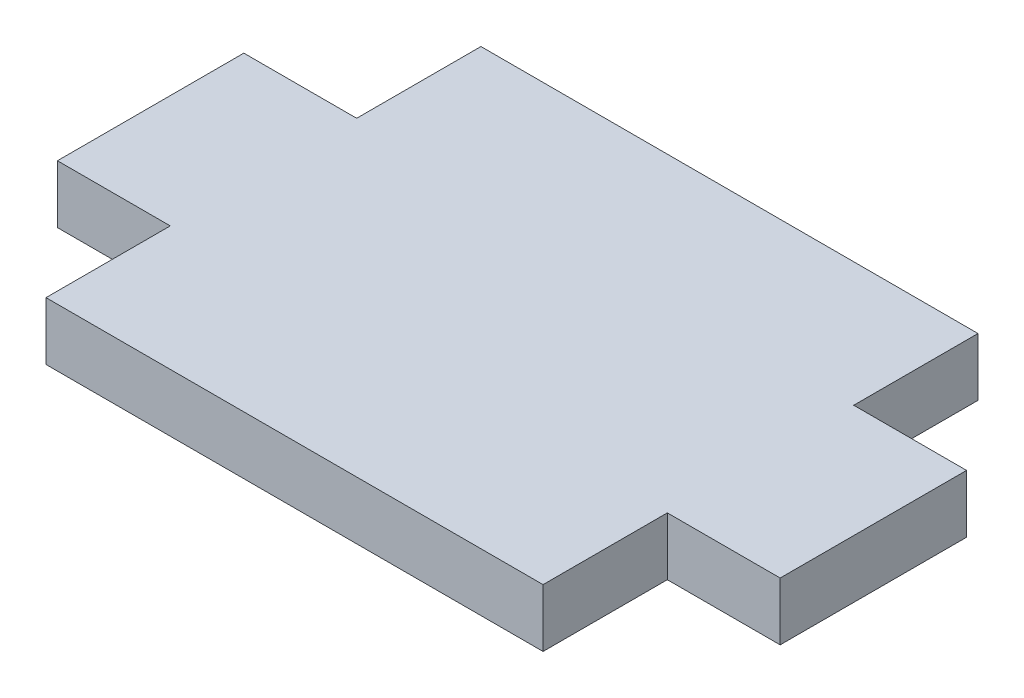
SolidWorks part; units mm, degrees
ref_plane "Front Plane" through (0, 0, 0) normal (0, 0, 1) x (1, 0, 0)
ref_plane "Top Plane" through (0, 0, 0) normal (0, 1, 0) x (1, 0, 0)
ref_plane "Right Plane" through (0, 0, 0) normal (1, 0, 0) x (0, 0, -1)
sketch "Sketch1" plane through (0, 0, 0) normal (0, 1, 0) x (1, 0, 0)
  line L0 (0, 4.0447) -> (0, -2.5708) construction
  line L1 (-12.7, 11.1125) -> (12.7, 11.1125)
  line L2 (-12.7, 11.1125) -> (-12.7, 4.7625)
  line L3 (-12.7, -11.1125) -> (12.7, -11.1125)
  line L4 (12.7, 11.1125) -> (12.7, 4.7625)
  line L5 (-12.7, 11.1125) -> (12.7, -11.1125) construction
  line L6 (-12.7, -11.1125) -> (12.7, 11.1125) construction
  line L7 (12.7, 4.7625) -> (18.4658, 4.7625)
  line L9 (12.7, -4.7625) -> (18.4658, -4.7625)
  line L10 (18.4658, 4.7625) -> (18.4658, -4.7625)
  line L11 (-12.7, -4.7625) -> (-18.4658, -4.7625)
  line L12 (-18.4658, 4.7625) -> (-18.4658, -4.7625)
  line L13 (-12.7, 4.7625) -> (-18.4658, 4.7625)
  line L14 (-12.7, -4.7625) -> (-12.7, -11.1125)
  line L15 (12.7, -4.7625) -> (12.7, -11.1125)
  point P0 (0, 0)
  point P10 (18.4658, 0)
  dimension "D1" = 5.7658
  dimension "D2" = 25.4
  dimension "D3" = 6.35
  dimension "D4" = 9.525
extrude "Boss-Extrude1" add sketch "Sketch1" along normal blind 2.9591
